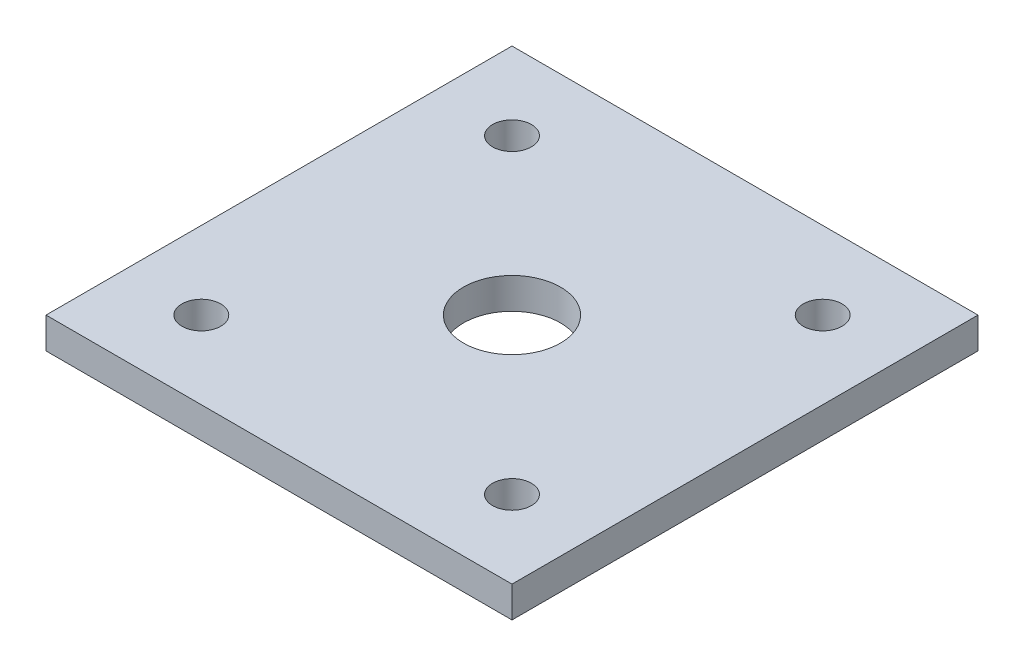
SolidWorks part; units mm, degrees
ref_plane "Front Plane" through (0, 0, 0) normal (0, 0, 1) x (1, 0, 0)
ref_plane "Top Plane" through (0, 0, 0) normal (0, 1, 0) x (1, 0, 0)
ref_plane "Right Plane" through (0, 0, 0) normal (1, 0, 0) x (0, 0, -1)
sketch "Sketch1" plane through (0, 0, 0) normal (0, 1, 0) x (1, 0, 0)
  line L0 (-60, 60) -> (60, -60)
  line L1 (-60, 60) -> (60, 60)
  line L2 (-60, 60) -> (-60, -60)
  line L3 (-60, -60) -> (60, -60)
  line L4 (60, 60) -> (60, -60)
  line L5 (60, 60) -> (-60, -60)
  point P4 (0, 0)
  dimension "D1" = 120
extrude "Boss-Extrude2" add sketch "Sketch1" along normal blind 8 contours L5 L1 L0 | L5 L0 L2 | L0 L5 L3 | L4 L5 L0
sketch "Sketch3" plane through (0, 8, 0) normal (0, 1, 0) x (1, 0, 0)
  circle A0 centre (0, 0) radius 12.5
  dimension "D1" = 25
extrude "Cut-Extrude1" cut sketch "Sketch3" against normal through all contours A0
sketch "Sketch4" plane through (0, 8, 0) normal (0, 1, 0) x (1, 0, 0)
  line L0 (-60, 60) -> (60, 60) construction
  line L2 (-60, 60) -> (-60, -60) construction
  circle A0 centre (-40, 40) radius 5
  dimension "D1" = 10
  dimension "D2" = 20
  dimension "D3" = 20
extrude "Cut-Extrude2" cut sketch "Sketch4" against normal through all contours A0
mirror "Mirror1" about plane through (0, 0, 0) normal (1, 0, 0) of "Cut-Extrude2"
mirror "Mirror2" about plane through (0, 0, 0) normal (0, 0, 1) of "Mirror1", "Cut-Extrude2"
